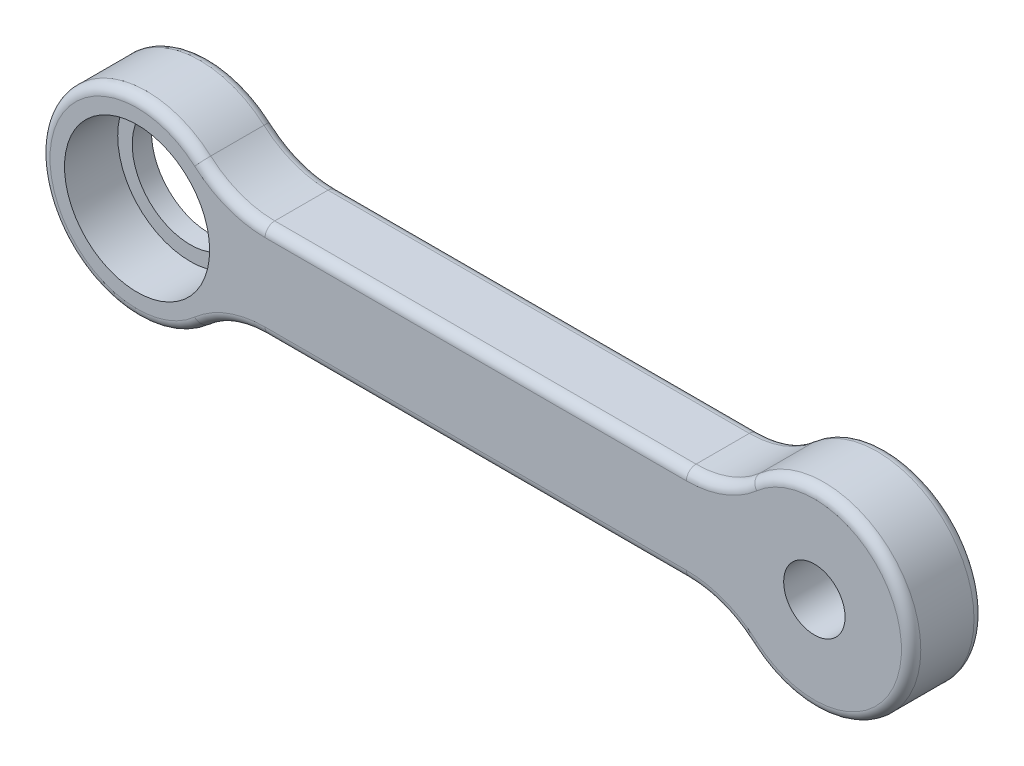
SolidWorks part; units mm, degrees
ref_plane "Front Plane" through (0, 0, 0) normal (0, 0, 1) x (1, 0, 0)
ref_plane "Top Plane" through (0, 0, 0) normal (0, 1, 0) x (1, 0, 0)
ref_plane "Right Plane" through (0, 0, 0) normal (1, 0, 0) x (0, 0, -1)
sketch "Sketch1" plane through (0, 0, 0) normal (0, 0, 1) x (1, 0, 0)
  line L0 (0, 5) -> (0, -5) construction
  line L1 (-21.7712, 5) -> (21.7712, 5)
  line L3 (-21.7712, -5) -> (21.7712, -5)
  line L5 (-35, 0) -> (35, 0) construction
  arc A0 (-28.3856, 7.5) -> (-28.3856, -7.5) centre (-35, 0) ccw
  arc A1 (28.3856, -7.5) -> (28.3856, 7.5) centre (35, 0) ccw
  arc A2 (21.7712, -5) -> (28.3856, -7.5) centre (21.7712, -15) cw
  arc A3 (21.7712, 5) -> (28.3856, 7.5) centre (21.7712, 15) ccw
  arc A4 (-28.3856, -7.5) -> (-21.7712, -5) centre (-21.7712, -15) cw
  arc A5 (-21.7712, 5) -> (-28.3856, 7.5) centre (-21.7712, 15) cw
  dimension "D2" = 20
  dimension "D4" = 10
  dimension "D1" = 70
  dimension "D3" = 10
extrude "Boss-Extrude1" add sketch "Sketch1" along normal blind 7.5
sketch "Sketch2" plane through (0, 0, 7.5) normal (0, 0, 1) x (1, 0, 0)
  circle A0 centre (-35, 0) radius 7.5
  dimension "D1" = 15
extrude "Cut-Extrude1" cut sketch "Sketch2" against normal offset from surface (5.5 mm away) 2 up to face at (0, 0, 0)
sketch "Sketch3" plane through (0, 0, 2) normal (0, 0, 1) x (1, 0, 0)
  circle A0 centre (-35, 0) radius 6
  dimension "D1" = 12
extrude "Cut-Extrude2" cut sketch "Sketch3" against normal through all
sketch "Sketch4" plane through (0, 0, 0) normal (0, 0, -1) x (-1, 0, 0)
  circle A0 centre (-35, 0) radius 3.175
  dimension "D1" = 6.35
extrude "Cut-Extrude3" cut sketch "Sketch4" against normal through all
fillet "Fillet1" radius 1 16 edges at (-25.3068, -5.6459, 0) (-45, 0, 0) (-25.3068, 5.6459, 0) (0, 5, 0) (25.3068, 5.6459, 0) (45, 0, 0) (25.3068, -5.6459, 0) (25.3068, 5.6459, 7.5) (45, 0, 7.5) (25.3068, -5.6459, 7.5) (0, -5, 7.5) (-25.3068, -5.6459, 7.5) (-45, 0, 7.5) (-25.3068, 5.6459, 7.5) (0, -5, 0) (0, 5, 7.5)
mirror "Mirror1" [suppressed] about plane through (0, 0, 0) normal (1, 0, 0)
